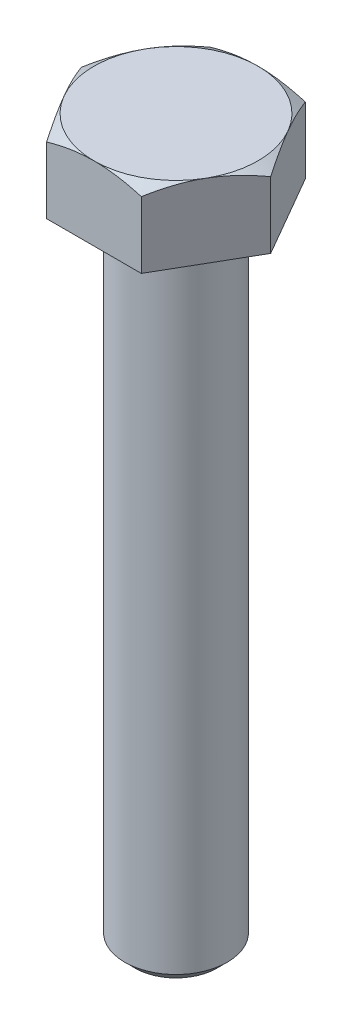
SolidWorks part; units mm, degrees
ref_plane "Front Plane" through (0, 0, 0) normal (0, 0, 1) x (1, 0, 0)
ref_plane "Top Plane" through (0, 0, 0) normal (0, 1, 0) x (1, 0, 0)
ref_plane "Right Plane" through (0, 0, 0) normal (1, 0, 0) x (0, 0, -1)
sketch "Sketch1" plane through (0, 0, 0) normal (0, 1, 0) x (1, 0, 0)
  line L1 (-2.3094, -4) -> (2.3094, -4)
  line L2 (2.3094, -4) -> (4.6188, 0)
  line L3 (4.6188, 0) -> (2.3094, 4)
  line L4 (2.3094, 4) -> (-2.3094, 4)
  line L5 (-2.3094, 4) -> (-4.6188, 0)
  line L6 (-4.6188, 0) -> (-2.3094, -4)
  circle A0 centre (0, 0) radius 4 construction
  dimension "D1" = 8
extrude "Boss-Extrude1" add sketch "Sketch1" along normal blind 3.6
sketch "Sketch2" plane through (0, 0, 0) normal (1, 0, 0) x (0, 0, -1)
  line L0 (8.3262, 1.1023) -> (4, 3.6)
  line L1 (4, 3.6) -> (8.3262, 3.6)
  line L4 (8.3262, 3.6) -> (8.3262, 1.1023)
  line L5 (0, 0) -> (0, 4.3378) construction
  dimension "D1" = 30
revolve "Cut-Revolve1" cut sketch "Sketch2" angle 360 about L5
sketch "Sketch3" plane through (0, 0, 0) normal (0, -1, 0) x (1, 0, 0)
  circle A0 centre (0, 0) radius 2.5
  dimension "D1" = 5
extrude "Boss-Extrude2" add sketch "Sketch3" along normal blind 31.5
cosmetic thread "Cosmetic Thread1" parameters "D2"=4.11
chamfer "Chamfer1" distance 0.5 angle 45 1 edges at (0, -31.5, -2.5)
fillet "Fillet1" radius 0.4 1 edges at (0, 0, -2.5)
